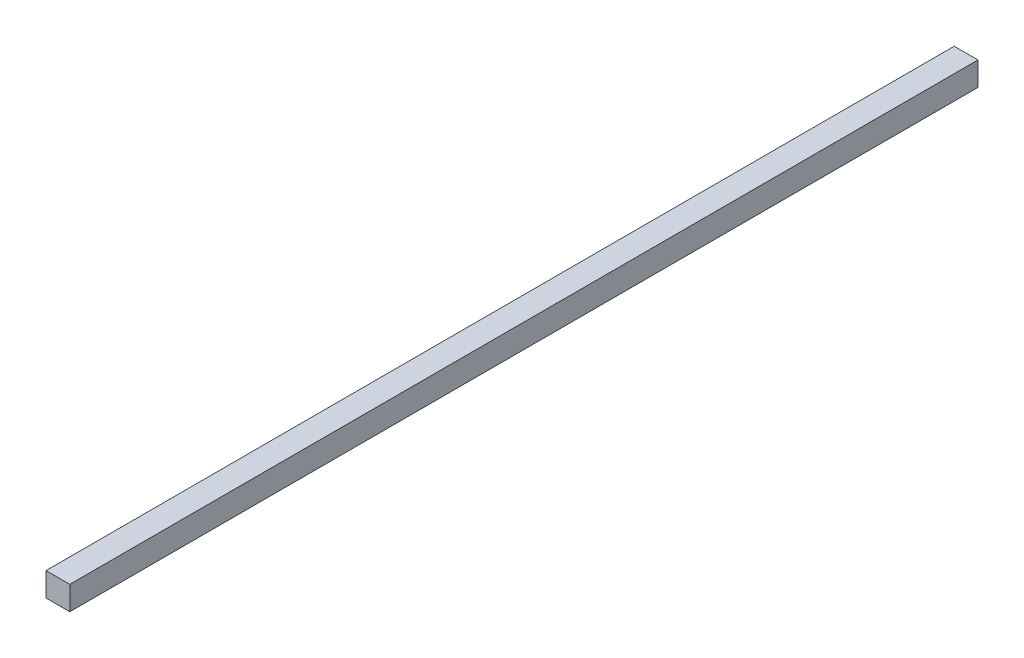
SolidWorks part; units mm, degrees
ref_plane "Front Plane" through (0, 0, 0) normal (0, 0, 1) x (1, 0, 0)
ref_plane "Top Plane" through (0, 0, 0) normal (0, 1, 0) x (1, 0, 0)
ref_plane "Right Plane" through (0, 0, 0) normal (1, 0, 0) x (0, 0, -1)
sketch "Sketch1" plane through (0, 0, 0) normal (0, 0, 1) x (1, 0, 0)
  line L1 (-10, -10) -> (10, -10)
  line L2 (-10, -10) -> (-10, 10)
  line L3 (-10, 10) -> (10, 10)
  line L4 (10, -10) -> (10, 10)
  line L5 (-10, -10) -> (10, 10) construction
  line L6 (-10, 10) -> (10, -10) construction
  point P0 (0, 0)
  dimension "D1" = 20
  dimension "D2" = 20
extrude "Boss-Extrude1" add sketch "Sketch1" along normal mid plane 764
